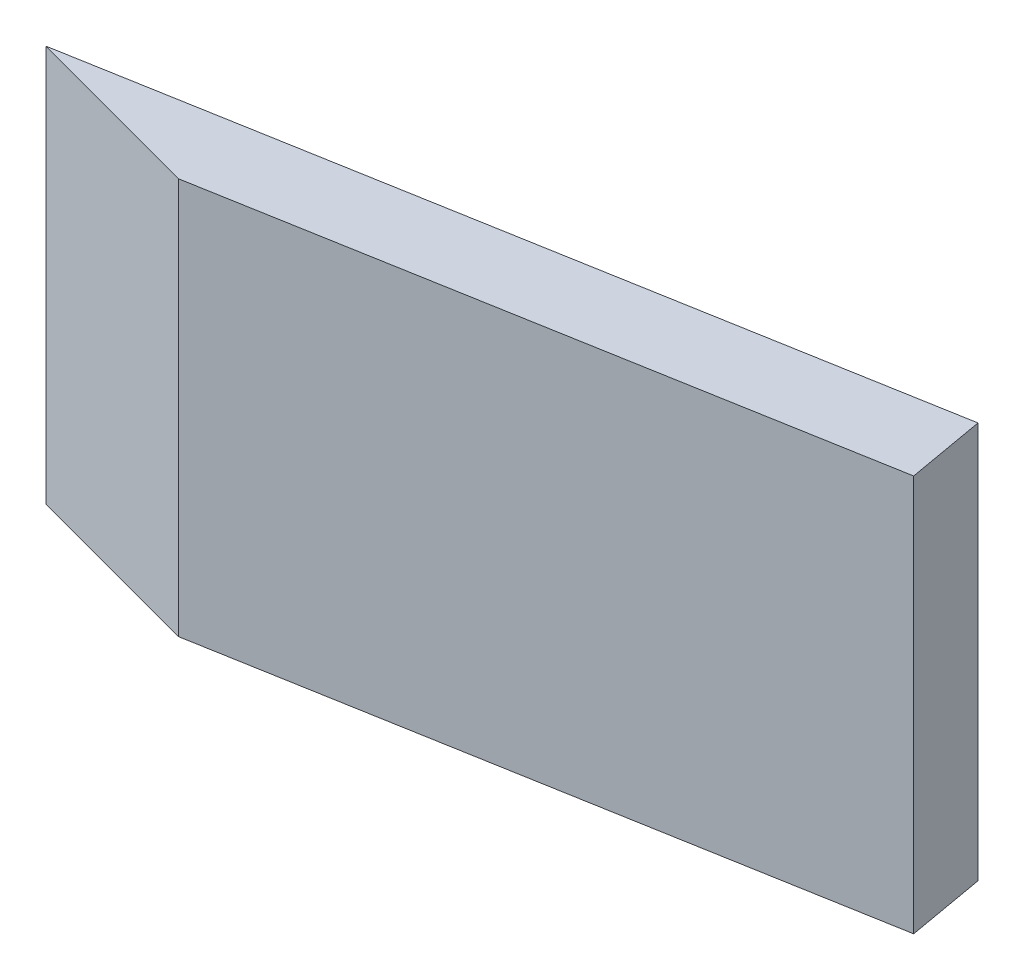
SolidWorks part; units mm, degrees
ref_plane "Front Plane" through (0, 0, 0) normal (0, 0, 1) x (1, 0, 0)
ref_plane "Top Plane" through (0, 0, 0) normal (0, 1, 0) x (1, 0, 0)
ref_plane "Right Plane" through (0, 0, 0) normal (1, 0, 0) x (0, 0, -1)
sketch "Sketch1" plane through (0, 0, 0) normal (0, 1, 0) x (1, 0, 0)
  line L0 (0, 0) -> (63.439, 11.186)
  line L1 (63.439, 11.186) -> (64.5416, 4.9325)
  line L2 (64.5416, 4.9325) -> (14.5134, -3.8889)
  line L3 (14.5134, -3.8889) -> (0, 0)
  line L4 (14.5134, -3.8889) -> (13.4107, 2.3647) construction
  line L5 (14.5134, -3.8889) -> (62.5932, -3.8889) construction
  point P3 (37.409, 0)
  dimension "D1" = 6.35
  dimension "D2" = 10
  dimension "D3" = 50.8
  dimension "D4" = 25
extrude "Boss-Extrude1" add sketch "Sketch1" along normal blind 31.75
